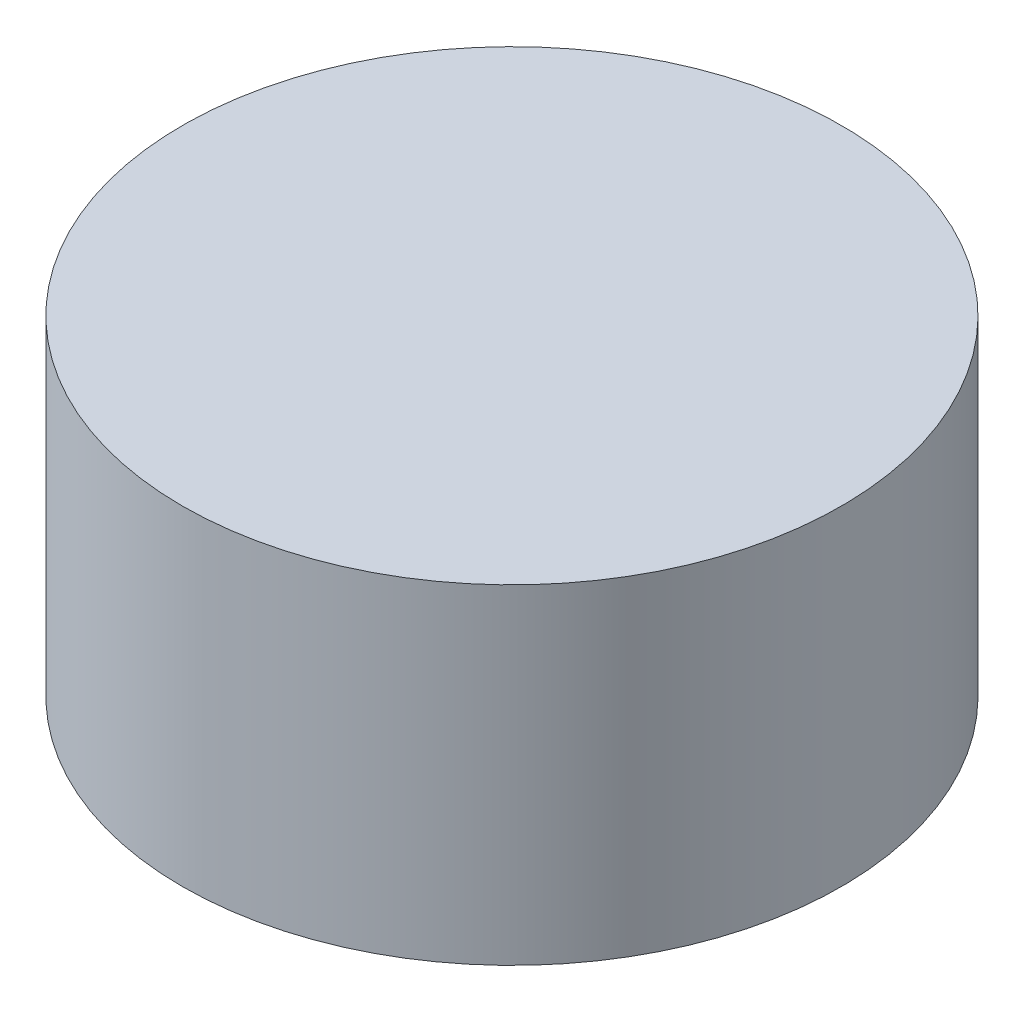
SolidWorks part; units mm, degrees
material "1023 Carbon Steel Sheet (SS)"
ref_plane "Front Plane" through (0, 0, 0) normal (0, 0, 1) x (1, 0, 0)
ref_plane "Top Plane" through (0, 0, 0) normal (0, 1, 0) x (1, 0, 0)
ref_plane "Right Plane" through (0, 0, 0) normal (1, 0, 0) x (0, 0, -1)
sketch "Sketch1" plane through (0, 0, 0) normal (0, 1, 0) x (1, 0, 0)
  circle A0 centre (0, 0) radius 3.175
  dimension "D1" = 6.35
extrude "Boss-Extrude1" add sketch "Sketch1" along normal mid plane 3.175
